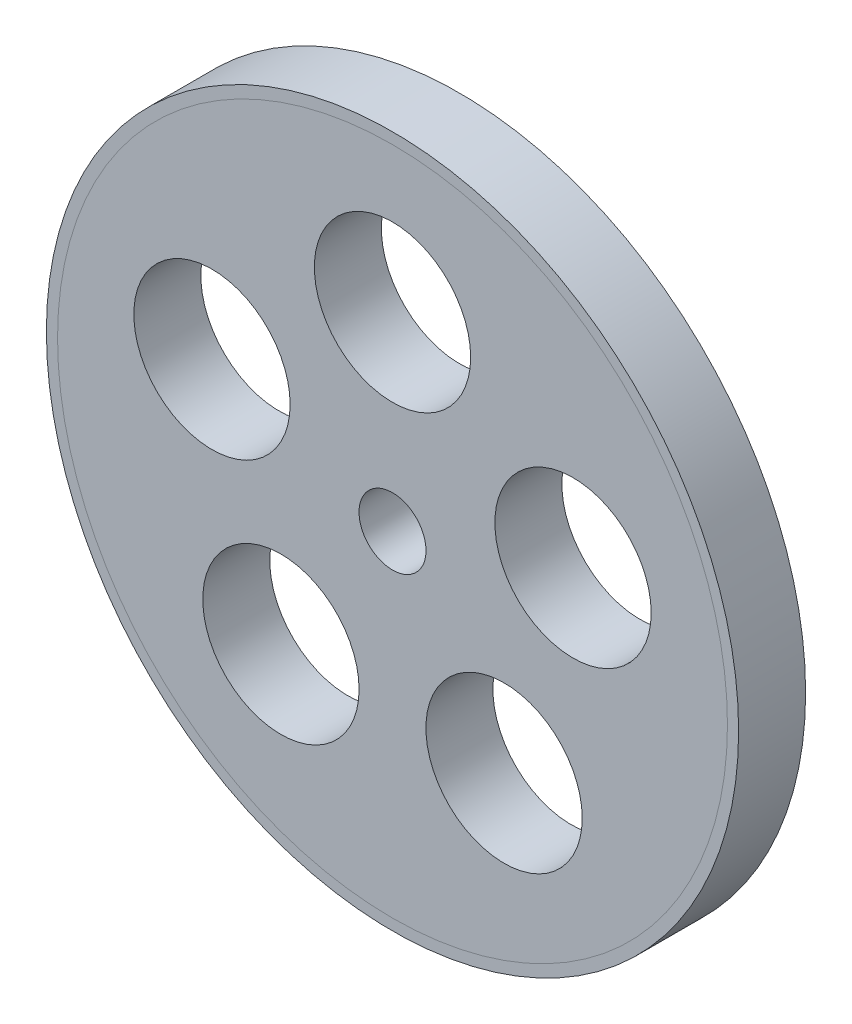
SolidWorks part; units mm, degrees
ref_plane "Front Plane" through (0, 0, 0) normal (0, 0, 1) x (1, 0, 0)
ref_plane "Top Plane" through (0, 0, 0) normal (0, 1, 0) x (1, 0, 0)
ref_plane "Right Plane" through (0, 0, 0) normal (1, 0, 0) x (0, 0, -1)
sketch "Sketch1" plane through (0, 0, 0) normal (0, 0, 1) x (1, 0, 0)
  circle A0 centre (0, 0) radius 15
  circle A1 centre (0, 0) radius 1.5
  dimension "D1" = 30
  dimension "D2" = 3
extrude "Boss-Extrude1" add sketch "Sketch1" along normal blind 3
sketch "Sketch4" plane through (0, 0, 3) normal (0, 0, 1) x (1, 0, 0)
  line L0 (0, 0) -> (0, 15) construction
  circle A0 centre (0, 0) radius 12
  circle A1 centre (0, 0) radius 5
  circle A2 centre (0, 0) radius 15 construction
  circle A3 centre (0, 8.5) radius 3.5
  circle A4 centre (8.084, 2.6266) radius 3.5
  circle A5 centre (4.9962, -6.8766) radius 3.5
  circle A6 centre (-4.9962, -6.8766) radius 3.5
  circle A7 centre (-8.084, 2.6266) radius 3.5
  point P20 (0, 0)
  dimension "D1" = 24
  dimension "D2" = 10
  dimension "D3" = 5
extrude "Cut-Extrude1" cut sketch "Sketch4" against normal through all both and the other way through all contours A4 | A3 L0 | L0 A3 | A7 | A6 | A5
sketch "Sketch2" plane through (0, 0, 0) normal (0, 1, 0) x (1, 0, 0)
  line L0 (-15, -3) -> (15, -3) construction
  line L1 (-15, 0) -> (-15.5, 0)
  line L2 (-15, 0) -> (-15, -3)
  line L3 (-15, -3) -> (-15.5, -3)
  line L4 (-15.5, 0) -> (-15.5, -3)
  line L5 (0, 0) -> (0, -3) construction
  dimension "D1" = 0.5
revolve "Revolve1" add sketch "Sketch2" angle 360 about L5
